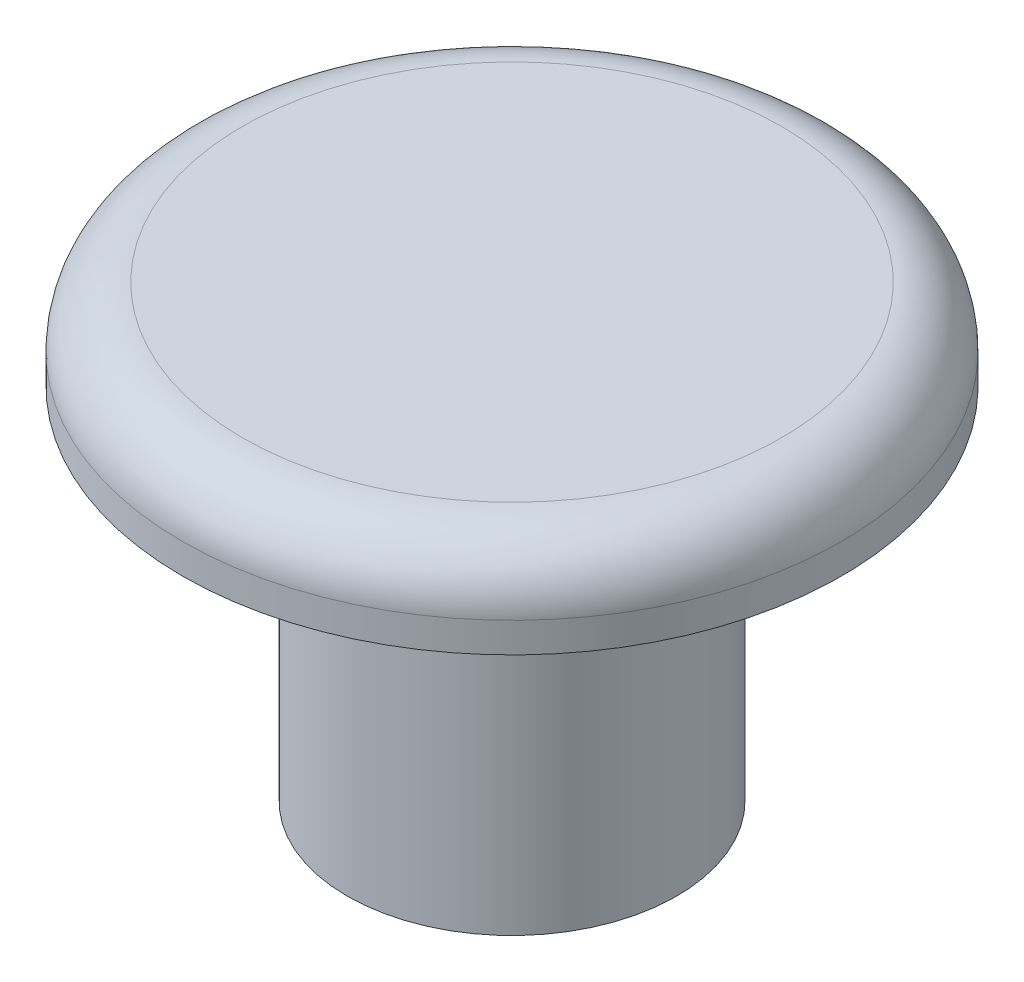
SolidWorks part; units mm, degrees
ref_plane "Front Plane" through (0, 0, 0) normal (0, 0, 1) x (1, 0, 0)
ref_plane "Top Plane" through (0, 0, 0) normal (0, 1, 0) x (1, 0, 0)
ref_plane "Right Plane" through (0, 0, 0) normal (1, 0, 0) x (0, 0, -1)
sketch "Sketch2" plane through (0, 0, 0) normal (0, 0, 1) x (1, 0, 0)
  line L0 (0, 0) -> (-5.5, 0)
  line L1 (-5.5, 0) -> (-5.5, 12)
  line L2 (0, 0) -> (0, -50000) construction
  line L3 (-5.5, 12) -> (-11, 12)
  line L4 (-11, 12) -> (-11, 13)
  line L5 (-9, 15) -> (0, 15)
  line L6 (0, 15) -> (0, 0)
  arc A0 (-11, 13) -> (-9, 15) centre (-9, 13) cw
  point P11 (-11, 15)
  dimension "D5" = 2
  dimension "D1" = 5.5
  dimension "D2" = 12
  dimension "D3" = 11
  dimension "D4" = 3
revolve "Revolve1" add sketch "Sketch2" angle 360 about L2
